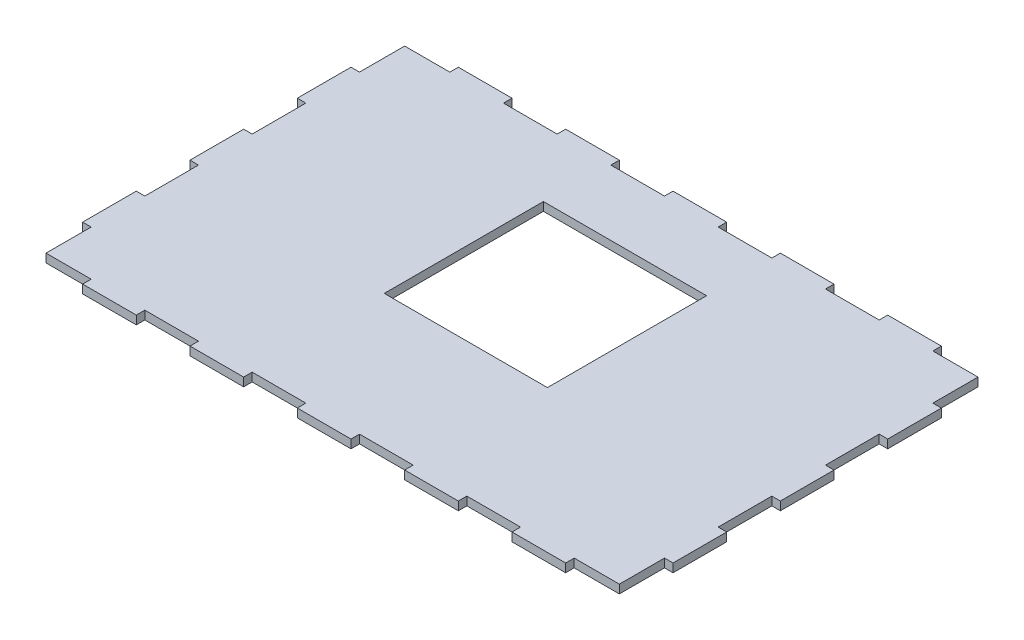
SolidWorks part; units mm, degrees
material "Acrylic (Medium-high impact)"
ref_plane "Front Plane" through (0, 0, 0) normal (0, 0, 1) x (1, 0, 0)
ref_plane "Top Plane" through (0, 0, 0) normal (0, 1, 0) x (1, 0, 0)
ref_plane "Right Plane" through (0, 0, 0) normal (1, 0, 0) x (0, 0, -1)
sketch "Sketch40" plane through (0, 0, 0) normal (0, 1, 0) x (1, 0, 0)
  line L2 (110, -738.1019) -> (-110, -738.1019)
  line L3 (110, -738.1019) -> (110, -598.1019)
  line L4 (110, -598.1019) -> (-110, -598.1019)
  line L5 (-110, -738.1019) -> (-110, -598.1019)
extrude "Boss-Extrude7" add sketch "Sketch40" along normal blind 3.175 separate body
sketch "Sketch41" plane through (0, 3.175, 0) normal (0, 1, 0) x (1, 0, 0)
  line L0 (70, -738.1019) -> (70, -734.9269)
  line L1 (-110, -738.1019) -> (110, -738.1019) construction
  line L2 (70, -738.1019) -> (50, -738.1019)
  line L3 (50, -738.1019) -> (50, -734.9269)
  line L4 (110, -738.1019) -> (90, -738.1019)
  line L7 (90, -738.1019) -> (90, -734.9269)
  line L8 (70, -734.9269) -> (50, -734.9269)
  line L9 (30, -738.1019) -> (30, -734.9269)
  line L10 (30, -738.1019) -> (10, -738.1019)
  line L11 (10, -738.1019) -> (10, -734.9269)
  line L12 (30, -734.9269) -> (10, -734.9269)
  line L13 (-10, -738.1019) -> (-10, -734.9269)
  line L14 (-10, -738.1019) -> (-30, -738.1019)
  line L15 (-30, -738.1019) -> (-30, -734.9269)
  line L16 (-10, -734.9269) -> (-30, -734.9269)
  line L17 (-50, -738.1019) -> (-50, -734.9269)
  line L18 (-50, -738.1019) -> (-70, -738.1019)
  line L19 (-70, -738.1019) -> (-70, -734.9269)
  line L20 (-50, -734.9269) -> (-70, -734.9269)
  line L21 (-90, -738.1019) -> (-90, -734.9269)
  line L22 (-90, -738.1019) -> (-110, -738.1019)
  line L25 (70, -598.1019) -> (70, -601.2769)
  line L26 (110, -598.1019) -> (-110, -598.1019) construction
  line L27 (70, -598.1019) -> (50, -598.1019)
  line L28 (50, -598.1019) -> (50, -601.2769)
  line L29 (110, -598.1019) -> (90, -598.1019)
  line L32 (90, -598.1019) -> (90, -601.2769)
  line L33 (70, -601.2769) -> (50, -601.2769)
  line L34 (30, -598.1019) -> (30, -601.2769)
  line L35 (30, -598.1019) -> (10, -598.1019)
  line L36 (10, -598.1019) -> (10, -601.2769)
  line L37 (30, -601.2769) -> (10, -601.2769)
  line L38 (-10, -598.1019) -> (-10, -601.2769)
  line L39 (-10, -598.1019) -> (-30, -598.1019)
  line L40 (-30, -598.1019) -> (-30, -601.2769)
  line L41 (-10, -601.2769) -> (-30, -601.2769)
  line L42 (-50, -598.1019) -> (-50, -601.2769)
  line L43 (-50, -598.1019) -> (-70, -598.1019)
  line L44 (-70, -598.1019) -> (-70, -601.2769)
  line L45 (-50, -601.2769) -> (-70, -601.2769)
  line L46 (-90, -598.1019) -> (-90, -601.2769)
  line L47 (-90, -598.1019) -> (-110, -598.1019)
  line L50 (106.825, -618.1019) -> (106.825, -601.2769)
  line L51 (110, -738.1019) -> (110, -598.1019) construction
  line L52 (110, -618.1019) -> (106.825, -618.1019)
  line L53 (106.825, -601.2769) -> (90, -601.2769)
  line L54 (110, -598.1019) -> (110, -618.1019)
  line L55 (110, -738.1019) -> (110, -718.1019)
  line L56 (110, -718.1019) -> (106.825, -718.1019)
  line L57 (106.825, -718.1019) -> (106.825, -734.9269)
  line L58 (106.825, -734.9269) -> (90, -734.9269)
  line L60 (110, -658.1019) -> (110, -638.1019)
  line L61 (110, -658.1019) -> (106.825, -658.1019)
  line L62 (106.825, -658.1019) -> (106.825, -638.1019)
  line L63 (110, -698.1019) -> (106.825, -698.1019)
  line L64 (110, -698.1019) -> (110, -678.1019)
  line L65 (110, -678.1019) -> (106.825, -678.1019)
  line L66 (106.825, -698.1019) -> (106.825, -678.1019)
  line L67 (110, -638.1019) -> (106.825, -638.1019)
  line L68 (-110, -738.1019) -> (-110, -718.1019)
  line L69 (-110, -598.1019) -> (-110, -738.1019) construction
  line L70 (-110, -718.1019) -> (-106.825, -718.1019)
  line L71 (-106.825, -718.1019) -> (-106.825, -734.9269)
  line L72 (-90, -734.9269) -> (-106.825, -734.9269)
  line L73 (-110, -738.1019) -> (-110, -734.9269) [skipped]
  line L74 (-110, -598.1019) -> (-110, -618.1019)
  line L75 (-110, -618.1019) -> (-106.825, -618.1019)
  line L76 (-106.825, -618.1019) -> (-106.825, -601.2769)
  line L77 (-106.825, -601.2769) -> (-90, -601.2769)
  line L78 (-110, -598.1019) -> (-110, -601.2769) [skipped]
  line L79 (-110, -658.1019) -> (-110, -638.1019)
  line L80 (-110, -658.1019) -> (-106.825, -658.1019)
  line L81 (-106.825, -658.1019) -> (-106.825, -638.1019)
  line L82 (-110, -698.1019) -> (-106.825, -698.1019)
  line L83 (-110, -698.1019) -> (-110, -678.1019)
  line L84 (-110, -678.1019) -> (-106.825, -678.1019)
  line L85 (-106.825, -698.1019) -> (-106.825, -678.1019)
  line L86 (-110, -638.1019) -> (-106.825, -638.1019)
  dimension "D1" = 6
  dimension "D2" = 6
  dimension "D3" = 2
  dimension "D4" = 2
extrude "Cut-Extrude21" cut sketch "Sketch41" against normal blind 3.175
sketch "Sketch53" plane through (0, 3.175, 0) normal (0, 1, 0) x (1, 0, 0)
  line L1 (-30.8, -625.6019) -> (30, -625.6019)
  line L6 (30, -625.6019) -> (30, -684.9019)
  line L7 (30, -684.9019) -> (-30.8, -684.9019)
  line L8 (-30.8, -684.9019) -> (-30.8, -625.6019)
extrude "Cut-Extrude26" cut sketch "Sketch53" against normal blind 3.175
